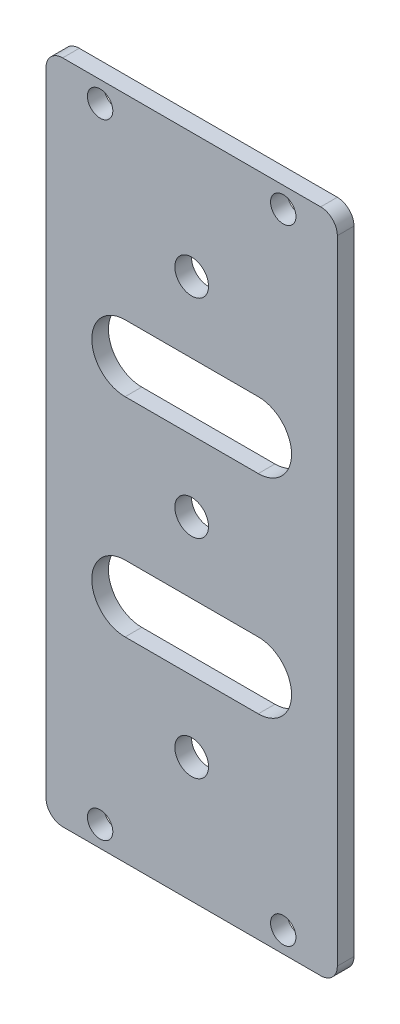
SolidWorks part; units mm, degrees
material "Thornel Mat VMA"
ref_plane "前视基准面" through (0, 0, 0) normal (0, 0, 1) x (1, 0, 0)
ref_plane "上视基准面" through (0, 0, 0) normal (0, 1, 0) x (1, 0, 0)
ref_plane "右视基准面" through (0, 0, 0) normal (1, 0, 0) x (0, 0, -1)
other "Configuration Table"
sketch "草图1" plane through (0, 0, 0) normal (0, 0, 1) x (1, 0, 0)
  line L1 (-17.5, -40) -> (17.5, -40)
  line L2 (-17.5, -40) -> (-17.5, 40)
  line L3 (-17.5, 40) -> (17.5, 40)
  line L4 (17.5, -40) -> (17.5, 40)
  line L5 (-17.5, -40) -> (17.5, 40) construction
  line L6 (-17.5, 40) -> (17.5, -40) construction
  point P0 (0, 0)
  dimension "D1" = 35
  dimension "D2" = 80
extrude "凸台-拉伸1" add sketch "草图1" along normal blind 2
sketch "草图2" plane through (0, 0, 2) normal (0, 0, 1) x (1, 0, 0)
  line L1 (-11, -37.5) -> (11, -37.5) construction
  line L2 (-11, -37.5) -> (-11, 37.5) construction
  line L3 (-11, 37.5) -> (11, 37.5) construction
  line L4 (11, -37.5) -> (11, 37.5) construction
  line L5 (-11, -37.5) -> (11, 37.5) construction
  line L6 (-11, 37.5) -> (11, -37.5) construction
  circle A0 centre (11, 37.5) radius 1.525
  circle A1 centre (-11, 37.5) radius 1.525
  circle A2 centre (-11, -37.5) radius 1.525
  circle A3 centre (11, -37.5) radius 1.525
  point P0 (0, 0)
  dimension "D3" = 3.05
  dimension "D1" = 75
  dimension "D2" = 22
extrude "切除-拉伸1" cut sketch "草图2" against normal blind 2
fillet "圆角1" radius 2 4 edges at (17.5, -40, 1) (-17.5, -40, 1) (17.5, 40, 1) (-17.5, 40, 1)
sketch "草图3" plane through (0, 0, 2) normal (0, 0, 1) x (1, 0, 0)
  line L0 (0, 0) -> (2.025, 0) construction
  circle A0 centre (0, 25) radius 2.025
  circle A1 centre (0, 0) radius 2.025
  circle A2 centre (0, -25) radius 2.025
  dimension "D1" = 4.05
  dimension "D2" = 50
extrude "切除-拉伸2" cut sketch "草图3" against normal blind 10
sketch "草图4" plane through (0, 0, 2) normal (0, 0, 1) x (1, 0, 0)
  line L0 (-8, 12.5) -> (8, 12.5) construction
  line L1 (-8, 16.5) -> (8, 16.5)
  line L2 (-8, 8.5) -> (8, 8.5)
  line L3 (0, 0) -> (0, 25) construction
  line L4 (0, 0) -> (17.5, 0) construction
  line L5 (17.5, -38) -> (17.5, 38) construction
  line L6 (-8, -12.5) -> (8, -12.5) construction
  line L7 (-8, -16.5) -> (8, -16.5)
  line L8 (-8, -8.5) -> (8, -8.5)
  line L9 (0, 0) -> (0, -25) construction
  arc A0 (-8, 16.5) -> (-8, 8.5) centre (-8, 12.5) ccw
  arc A1 (8, 8.5) -> (8, 16.5) centre (8, 12.5) ccw
  arc A2 (-8, -16.5) -> (-8, -8.5) centre (-8, -12.5) cw
  arc A3 (8, -8.5) -> (8, -16.5) centre (8, -12.5) cw
  point P2 (0, 12.5)
  point P16 (0, -12.5)
  dimension "D2" = 4
  dimension "D1" = 16
extrude "切除-拉伸3" cut sketch "草图4" against normal through all both
